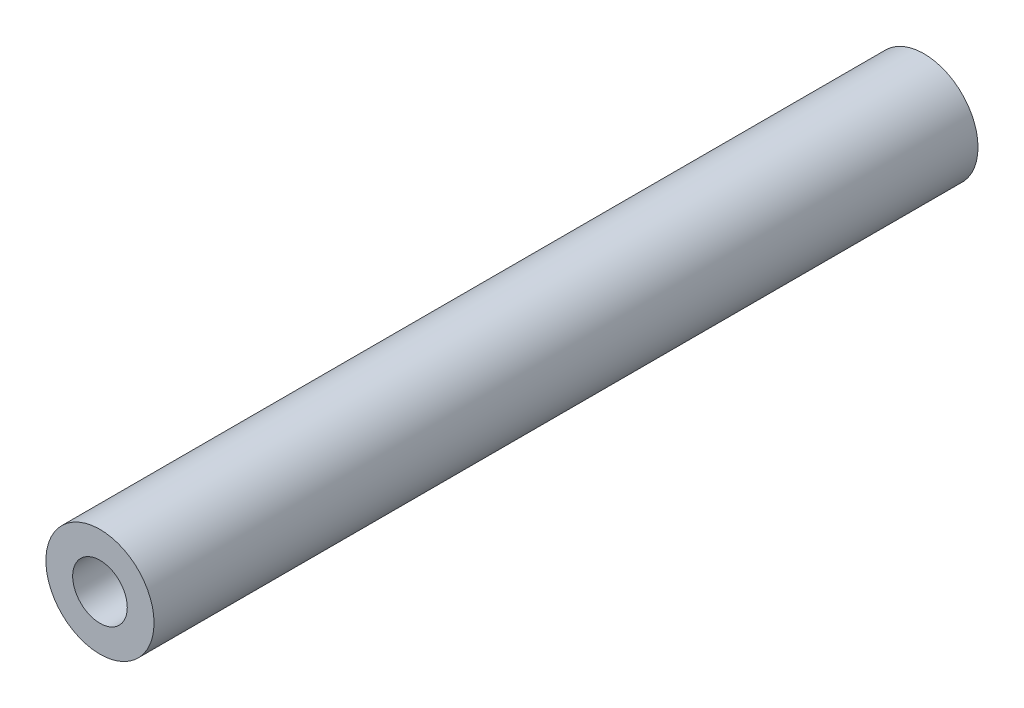
SolidWorks part; units mm, degrees
ref_plane "Front Plane" through (0, 0, 0) normal (0, 0, 1) x (1, 0, 0)
ref_plane "Top Plane" through (0, 0, 0) normal (0, 1, 0) x (1, 0, 0)
ref_plane "Right Plane" through (0, 0, 0) normal (1, 0, 0) x (0, 0, -1)
sketch "Sketch1" plane through (0, 0, 0) normal (0, 0, 1) x (1, 0, 0)
  circle A1 centre (0, 0) radius 5
  dimension "D2" = 10
extrude "Boss-Extrude1" add sketch "Sketch1" along normal blind 76.2
sketch "Sketch2" plane through (0, 0, 76.2) normal (0, 0, 1) x (1, 0, 0)
  circle A1 centre (0, 0) radius 2.525
  circle A2 centre (0, 0) radius 5 construction
  dimension "D1" = 5.05
extrude "Cut-Extrude1" cut sketch "Sketch2" against normal blind 6
ref_plane "Plane1" through (0, 0, 38.1) normal (0, 0, -1) x (-1, 0, 0)
mirror "Mirror1" about plane through (0, 0, 38.1) normal (0, 0, -1) of "Cut-Extrude1"
